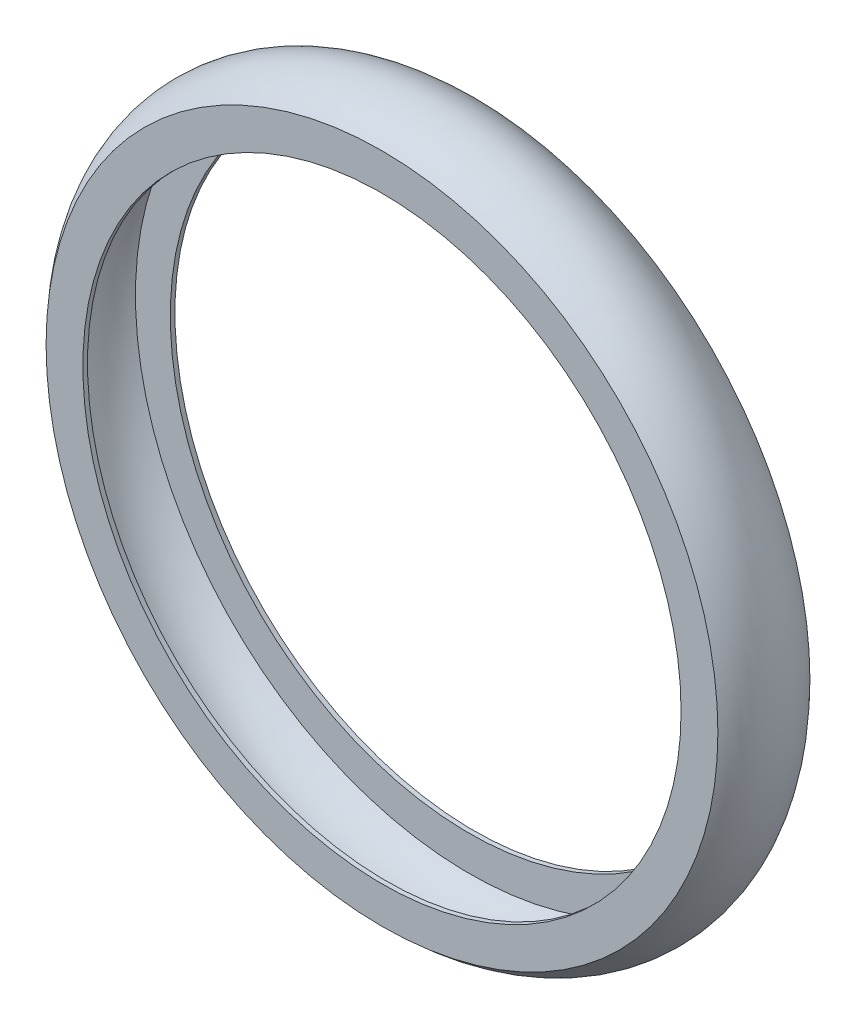
SolidWorks part; units mm, degrees
material "Silicon Rubber"
ref_plane "Front Plane" through (0, 0, 0) normal (0, 0, 1) x (1, 0, 0)
ref_plane "Top Plane" through (0, 0, 0) normal (0, 1, 0) x (1, 0, 0)
ref_plane "Right Plane" through (0, 0, 0) normal (1, 0, 0) x (0, 0, -1)
other "Configuration Table"
sketch "Sketch1" plane through (0, 0, 0) normal (1, 0, 0) x (0, 0, -1)
  line L0 (0, 0) -> (0, -47.4425) construction
  line L1 (-75.4215, 0) -> (101.6973, 0) construction
  line L2 (-50.8, 165.1) -> (-50.8, 185.42)
  line L3 (0, 165.1) -> (0, 185.42)
  line L4 (-48.26, 165.1) -> (-48.26, 184.3452)
  line L5 (-2.54, 165.1) -> (-2.54, 184.3452)
  line L6 (-50.8, 165.1) -> (-48.26, 165.1)
  line L7 (-2.54, 165.1) -> (0, 165.1)
  arc A0 (-50.8, 185.42) -> (0, 185.42) centre (-25.4, 160.02) cw
  arc A1 (-48.26, 184.3452) -> (-2.54, 184.3452) centre (-25.4, 160.02) cw
  dimension "D3" = 330.2
  dimension "D1" = 20.32
  dimension "D2" = 50.8
  dimension "D4" = 2.54
revolve "Revolve2" add sketch "Sketch1" angle 360 about L1
equation "\"A\"= 3"
equation "\"B\"= 1"
